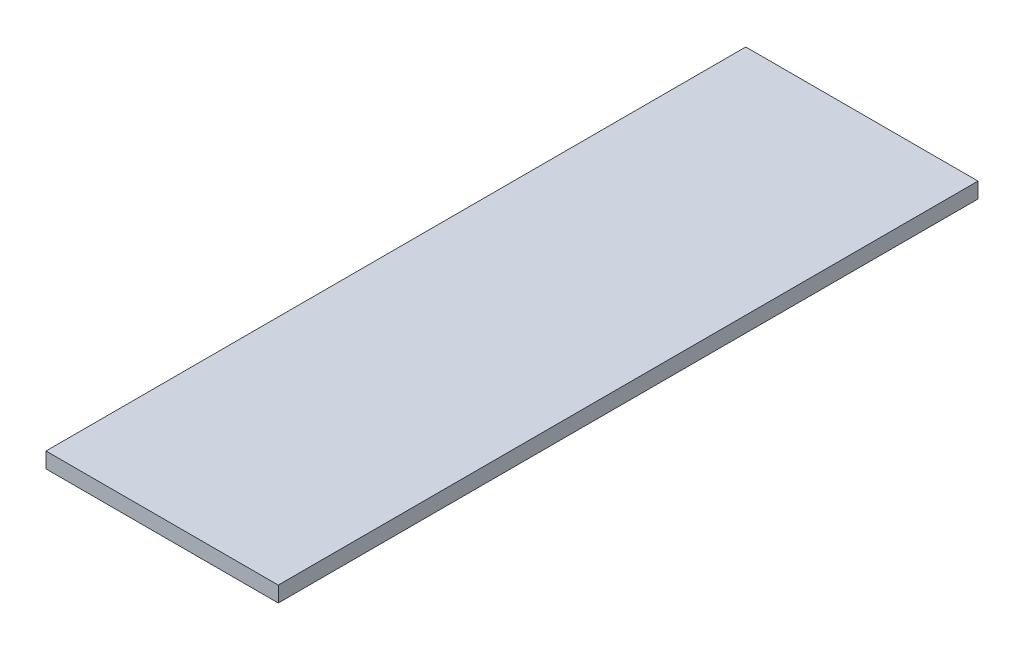
SolidWorks part; units mm, degrees
ref_plane "Ebene vorne" through (0, 0, 0) normal (0, 0, 1) x (1, 0, 0)
ref_plane "Ebene oben" through (0, 0, 0) normal (0, 1, 0) x (1, 0, 0)
ref_plane "Ebene rechts" through (0, 0, 0) normal (1, 0, 0) x (0, 0, -1)
sketch "Skizze1" plane through (0, 0, 0) normal (0, 0, 1) x (1, 0, 0)
  line L0 (182.5, 5) -> (182.5, -5)
  line L1 (331.8583, 5) -> (331.8583, -5)
  line L36 (182.5, 5) -> (331.8583, 5)
  line L37 (182.5, -5) -> (331.8583, -5)
extrude "Aufsatz-Linear austragen1" add sketch "Skizze1" along normal blind 450
